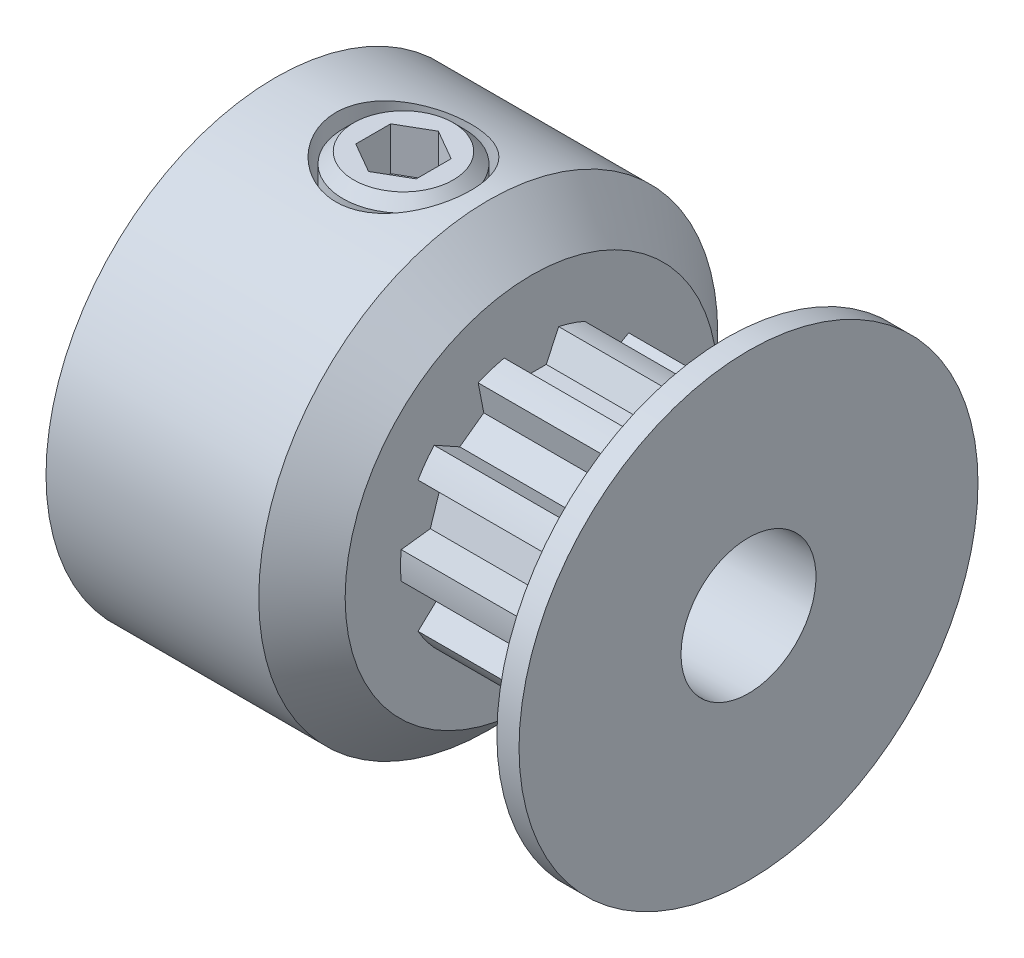
SolidWorks part; units mm, degrees
ref_plane "Front Plane" through (0, 0, 0) normal (0, 0, 1) x (1, 0, 0)
ref_plane "Top Plane" through (0, 0, 0) normal (0, 1, 0) x (1, 0, 0)
ref_plane "Right Plane" through (0, 0, 0) normal (1, 0, 0) x (0, 0, -1)
sketch "Sketch2" plane through (0, 0, 0) normal (1, 0, 0) x (0, 0, -1)
  line L3 (0, 0) -> (0, 2.413) construction
  line L6 (0, -2.921) -> (0, -3.2385) construction
  line L7 (-0.5715, 2.8645) -> (-0.3491, 2.3876)
  line L8 (0.5715, 2.8645) -> (0.3491, 2.3876)
  line L9 (-0.5715, 2.8645) -> (-0.6405, 3.0124)
  line L10 (0.5715, 2.8645) -> (0.6405, 3.0124)
  line L12 (-0.3491, 2.3876) -> (0.3491, 2.3876)
  line L14 (0, 2.921) -> (0, 3.2385) construction
  line L15 (0, 0) -> (0, -1.143) construction
  circle A0 centre (0, 0) radius 3.2385 construction
  circle A1 centre (0, 0) radius 2.413 construction
  circle A2 centre (0, 0) radius 2.921 construction
  arc A7 (0.6405, 3.0124) -> (-0.6405, 3.0124) centre (0, 0) ccw
  point P5 (0, 3.0798)
  dimension "D1" = 50
  dimension "PD" = 6.477
  dimension "D3" = 0.3175
  dimension "bt" = 1.143
  dimension "hs" = 1.143
  dimension "ht" = 0.508
sketch "Sketch1" plane through (0, 0, 0) normal (0, 0, 1) x (1, 0, 0)
  line L0 (-5.5626, 0) -> (5.5626, 0) construction
  line L1 (-5.5626, 1.5875) -> (5.5626, 1.5875)
  line L2 (-5.5626, 1.5875) -> (-5.5626, 5.3975)
  line L3 (-5.5626, 5.3975) -> (-0.5588, 5.3975)
  line L4 (-0.5588, 5.3975) -> (0.4572, 4.3815)
  line L5 (0.4572, 4.3815) -> (0.4572, 3.2385)
  line L6 (0.4572, 3.2385) -> (4.5212, 3.2385)
  line L7 (4.5212, 3.2385) -> (4.5212, 3.81)
  line L8 (4.5212, 3.2385) -> (5.5626, 3.2385) construction
  line L9 (5.0419, 5.3975) -> (5.5626, 5.3975)
  line L10 (5.5626, 5.3975) -> (5.5626, 1.5875)
  line L11 (5.0419, 3.2385) -> (5.0419, 5.3975) construction
  line L12 (-3.0607, 5.3975) -> (-3.0607, 1.5875) construction
  arc A0 (4.5212, 3.81) -> (5.0419, 5.3975) centre (7.2015, 3.81) cw
  dimension "D1" = 45
  dimension "Bore Size" = 3.175
  dimension "D2" = 6.477
  dimension "Overall Width" = 11.1252
  dimension "Inside Width" = 4.064
  dimension "Outside Width" = 5.1054
  dimension "Hub Dia" = 10.795
  dimension "OD" = 10.795
  dimension "D3" = 1.143
  dimension "D4" = 0.5715
revolve "Revolve1" add sketch "Sketch1" angle 360 about L0
sketch "Sketch4" plane through (0.4572, 0, 0) normal (1, 0, 0) x (0, 0, -1)
  circle A0 centre (0, 0) radius 3.0798
  circle A1 centre (0, 0) radius 3.2385 construction
  circle A2 centre (0, 0) radius 3.2385
extrude "Cut-Extrude2" cut sketch "Sketch4" along normal up to surface (4.064 mm away) up to face at (4.5212, 0, 3.2385)
sketch "Sketch3" plane through (0.4572, 0, 0) normal (1, 0, 0) x (0, 0, -1)
  line L2 (-0.5715, 2.8645) -> (-0.3491, 2.3876) construction
  line L3 (-0.3491, 2.3876) -> (0.3491, 2.3876) construction
  line L4 (0.5715, 2.8645) -> (0.3491, 2.3876) construction
  line L5 (-0.6405, 3.0124) -> (-0.3491, 2.3876)
  line L6 (-0.3491, 2.3876) -> (0.3491, 2.3876)
  line L7 (0.6405, 3.0124) -> (0.3491, 2.3876)
  arc A1 (0.6405, 3.0124) -> (-0.6405, 3.0124) centre (0, 0) ccw construction
  arc A2 (0.6405, 3.0124) -> (-0.6405, 3.0124) centre (0, 0) ccw
extrude "Cut-Extrude1" cut sketch "Sketch3" along normal up to surface (4.064 mm away) up to face at (4.5212, 0, 3.81)
pattern_circular "CirPattern1" count 10 over 360 about axis through (0, 0, 0) along (1, 0, 0) of "Cut-Extrude1"
sketch "Sketch5" plane through (0, 0, 0) normal (0, 0, 1) x (1, 0, 0)
  line L1 (4.5212, 3.81) -> (4.5212, -3.81) construction
  point P0 (4.5212, 0)
sketch "Sketch6" plane through (0, 0, 0) normal (0, 1, 0) x (1, 0, 0)
  line L0 (-5.5626, 0) -> (-4.1402, 0) construction
  line L1 (-5.5626, 5.3975) -> (-5.5626, -5.3975) construction
  line L2 (0.4572, 0) -> (-0.9652, 0) construction
  line L3 (0.4572, -0.3491) -> (0.4572, 0.3491) construction
  circle A0 centre (-2.5527, 0) radius 1.5875
  dimension "D1" = 3.175
extrude "Cut-Extrude3" cut sketch "Sketch6" along normal through all
sketch "Sketch7" plane through (0, 0, 0) normal (0, 0, 1) x (1, 0, 0)
  line L0 (-3.7211, 5.3975) -> (-2.5527, 5.3975)
  line L1 (-3.9751, 5.1435) -> (-3.9751, 2.2225)
  line L2 (-3.9751, 2.2225) -> (-3.7211, 1.9685)
  line L3 (-3.7211, 1.9685) -> (-2.5527, 1.9685)
  line L4 (-2.5527, 1.9685) -> (-2.5527, 5.3975) construction
  line L6 (-3.9751, 5.1435) -> (-3.7211, 5.3975)
  line L7 (-5.5626, 5.3975) -> (-0.5588, 5.3975) construction
  line L8 (-2.5527, 5.3975) -> (-2.5527, 1.9685)
  point P0 (-3.9751, 5.3975)
  point P4 (-3.9751, 1.9685)
  dimension "D1" = 2.8448
  dimension "D4" = 0.254
  dimension "D5" = 0.254
  dimension "D2" = 0.381
revolve "Revolve2" add sketch "Sketch7" angle 360 about L4
sketch "Sketch8" plane through (0, 5.3975, 0) normal (0, 1, 0) x (1, 0, 0)
  line L1 (-2.5527, 0.8212) -> (-3.2639, 0.4106)
  line L2 (-3.2639, 0.4106) -> (-3.2639, -0.4106)
  line L3 (-3.2639, -0.4106) -> (-2.5527, -0.8212)
  line L4 (-2.5527, -0.8212) -> (-1.8415, -0.4106)
  line L5 (-1.8415, -0.4106) -> (-1.8415, 0.4106)
  line L6 (-1.8415, 0.4106) -> (-2.5527, 0.8212)
  circle A0 centre (-2.5527, 0) radius 0.7112 construction
  dimension "D1" = 1.4224
extrude "Cut-Extrude4" cut sketch "Sketch8" against normal blind 1.016
pattern_circular "CirPattern2" [suppressed] count 2 over 90
pattern_circular "CirPattern3" [suppressed] count 2 over 90
equation "\"D3@Sketch2\" = (\"hs@Sketch2\"-\"ht@Sketch2\")/2"
equation "\"D2@Sketch1\" = \"PD@Sketch2\""
equation "\"D3@Sketch1\" = \"hs@Sketch2\""
equation "\"D4@Sketch1\" = \"D3@Sketch1\"/2"
